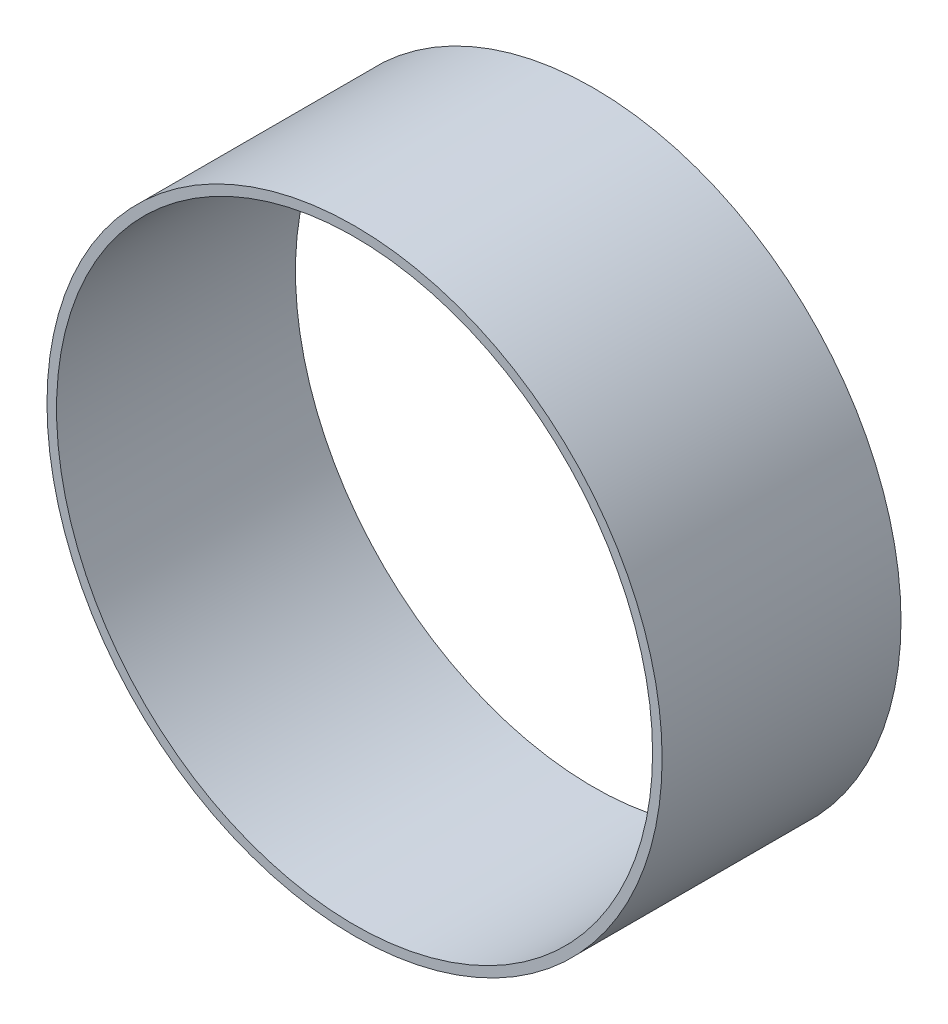
SolidWorks part; units mm, degrees
ref_plane "Front Plane" through (0, 0, 0) normal (0, 0, 1) x (1, 0, 0)
ref_plane "Top Plane" through (0, 0, 0) normal (0, 1, 0) x (1, 0, 0)
ref_plane "Right Plane" through (0, 0, 0) normal (1, 0, 0) x (0, 0, -1)
sketch "Sketch1" plane through (0, 0, 0) normal (0, 0, 1) x (1, 0, 0)
  circle A0 centre (0, 0) radius 65.405
  circle A1 centre (0, 0) radius 63.373
  dimension "D1" = 126.746
  dimension "D2" = 130.81
extrude "Boss-Extrude1" add sketch "Sketch1" along normal mid plane 50.8
equation "\"AIRFRAME_OD\"= 5.15in"
equation "\"AIRFRAME_ID\"= 4.99in"
equation "\"FLAT_T\"= 0.125in"
equation "\"NOSE_EXP_L\"= 27in"
equation "\"NOSE_SHOULDER_L\"= 5in"
equation "\"MAIN_L\"= 30in"
equation "\"RECO_COUP_L\"= 10in"
equation "\"RECO_SWITCH_L\"= 2in"
equation "\"DROGUE_L\"= 20in"
equation "\"ATS_FORE_COUP_L\"= 5.5in"
equation "\"ATS_AFT_COUP_L\"= 4.5in"
equation "\"LOWER_L\"= 30in"
equation "\"FIN_N\"= 4"
equation "\"CR_AFT_X\"= 0.5in"
equation "\"CR_FORE_X\"= 9.25in"
equation "\"D1@Sketch1\"=\"AIRFRAME_ID\""
equation "\"D2@Sketch1\"=\"AIRFRAME_OD\""
equation "\"D1@Boss-Extrude1\"=\"RECO_SWITCH_L\""
equation "\"FIN_ROOT\"= 8in"
equation "\"FIN_X\"= 0.75in"
equation "\"MOTOR_OD\"= 3.091in"
equation "\"MOTOR_ID\"= 3.00in"
equation "\"COUPLER_OD\"= 4.998in"
equation "\"COUPLER_ID\"= 4.85in"
equation "\"RECO_ROD_X\"= 3.5in"
equation "\"ATS_ROD_X\"= 3.75in"
equation "\"MOTOR_L\"= 14in"
equation "\"MOTOR_LOWER_X\"= 2in"
